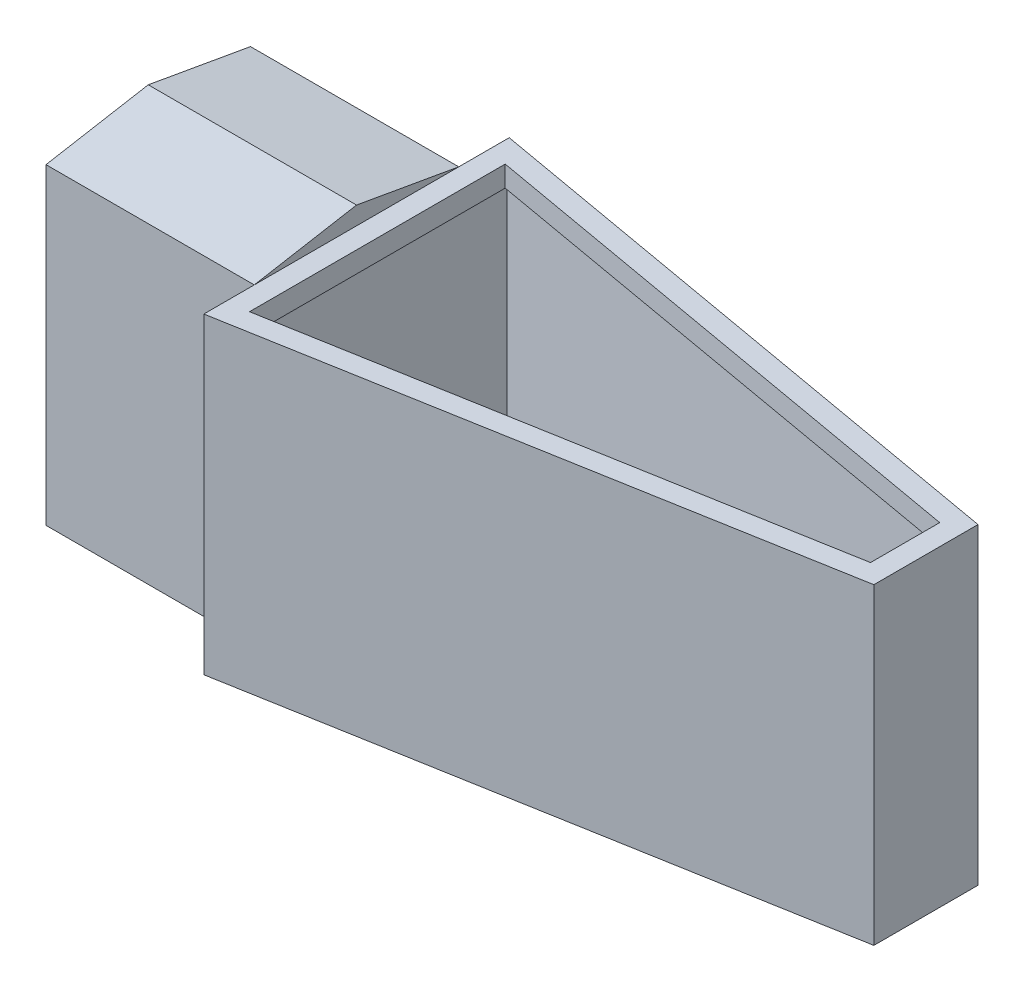
SolidWorks part; units mm, degrees
ref_plane "Front Plane" through (0, 0, 0) normal (0, 0, 1) x (1, 0, 0)
ref_plane "Top Plane" through (0, 0, 0) normal (0, 1, 0) x (1, 0, 0)
ref_plane "Right Plane" through (0, 0, 0) normal (1, 0, 0) x (0, 0, -1)
sketch "Sketch1" plane through (0, 0, 0) normal (0, 1, 0) x (1, 0, 0)
  line L5 (12.8538, 0.175) -> (12.8538, 37.417)
  line L7 (82.296, 12.446) -> (82.296, 25.146)
  line L8 (82.296, 25.146) -> (12.8538, 37.417)
  line L9 (82.296, 12.446) -> (12.8538, 0.175)
  point P0 (12.8538, 12.446)
  point P4 (12.7, 25.146)
  point P10 (82.296, 18.796)
  dimension "D8" = 12.7
extrude "Boss-Extrude1" add sketch "Sketch1" along normal blind 38.1
ref_plane "Plane1" through (0, 35.56, 0) normal (0, 1, 0) x (1, 0, 0)
sketch "Sketch3" plane through (0, 35.56, 0) normal (0, 1, 0) x (1, 0, 0)
  line L22 (79.756, 14.5765) -> (79.756, 23.0155)
  line L23 (79.756, 23.0155) -> (15.3938, 34.3888)
  line L24 (15.3938, 34.3888) -> (15.3938, 3.2032)
  line L25 (15.3938, 3.2032) -> (79.756, 14.5765)
  line L26 (79.756, 14.5765) -> (79.756, 23.0155)
  line L27 (79.756, 23.0155) -> (15.3938, 34.3888)
  line L28 (15.3938, 34.3888) -> (15.3938, 3.2032)
  line L29 (15.3938, 3.2032) -> (79.756, 14.5765)
  point P0 (15.24, 3.6938)
  dimension "D1" = 2.54
extrude "Cut-Extrude1" cut sketch "Sketch3" along normal up to surface (2.54 mm away) up to face at (47.5749, 38.1, -18.796)
sketch "Sketch6" plane through (0, 35.56, 0) normal (0, 1, 0) x (1, 0, 0)
  line L27 (81.026, 13.5113) -> (81.026, 24.0807)
  line L28 (14.1238, 1.6891) -> (81.026, 13.5113)
  line L29 (14.1238, 35.9029) -> (14.1238, 1.6891)
  line L30 (81.026, 24.0807) -> (14.1238, 35.9029)
  line L31 (81.026, 13.5113) -> (81.026, 24.0807)
  line L32 (14.1238, 1.6891) -> (81.026, 13.5113)
  line L33 (14.1238, 35.9029) -> (14.1238, 1.6891)
  line L34 (81.026, 24.0807) -> (14.1238, 35.9029)
  dimension "D1" = 1.27
extrude "Cut-Extrude2" cut sketch "Sketch6" against normal offset from surface (34.29 mm away) 1.27 up to face at (47.5749, 0, -18.796)
sketch "Sketch8" plane through (12.8538, 0, 0) normal (-1, 0, 0) x (0, 0, 1)
  line L0 (-0.175, 0) -> (-37.417, 38.1)
  line L1 (-37.417, 0) -> (-0.175, 38.1)
  line L2 (-18.796, 35.9014) -> (-18.796, 7.9304)
  line L4 (-31.265, 38.1) -> (-31.265, 0)
  line L6 (-6.327, 0) -> (-6.327, 38.1)
  line L7 (-18.796, 35.9014) -> (-31.265, 38.1)
  line L8 (-31.265, 38.1) -> (-6.327, 38.1)
  line L9 (-6.327, 38.1) -> (-18.796, 35.9014)
  line L10 (-18.796, 19.05) -> (-51.4552, 19.05) construction
  line L11 (-6.327, 0) -> (-18.796, 2.1986)
  line L12 (-31.265, 0) -> (-6.327, 0)
  line L13 (-3.1824, 31.519) -> (-31.0729, 31.519) [skipped]
  line L14 (-18.796, 2.1986) -> (-31.265, 0)
  line L15 (-30.9802, 6.581) -> (-2.9288, 6.581) [skipped]
  line L16 (-6.327, 38.1) -> (-18.796, 40.2986)
  line L17 (-18.796, 40.2986) -> (-31.265, 38.1)
  circle A0 centre (-18.796, 19.05) radius 13.9452 construction
  point P16 (-4.4855, 3.1266)
  point P17 (-18.796, 32.9952)
  point P20 (0, 0)
  dimension "D1" = 80
  dimension "D2" = 80
  dimension "D3" = 24.938
  dimension "D4" = 38.1
extrude "Boss-Extrude2" add sketch "Sketch8" along normal blind 25.4
